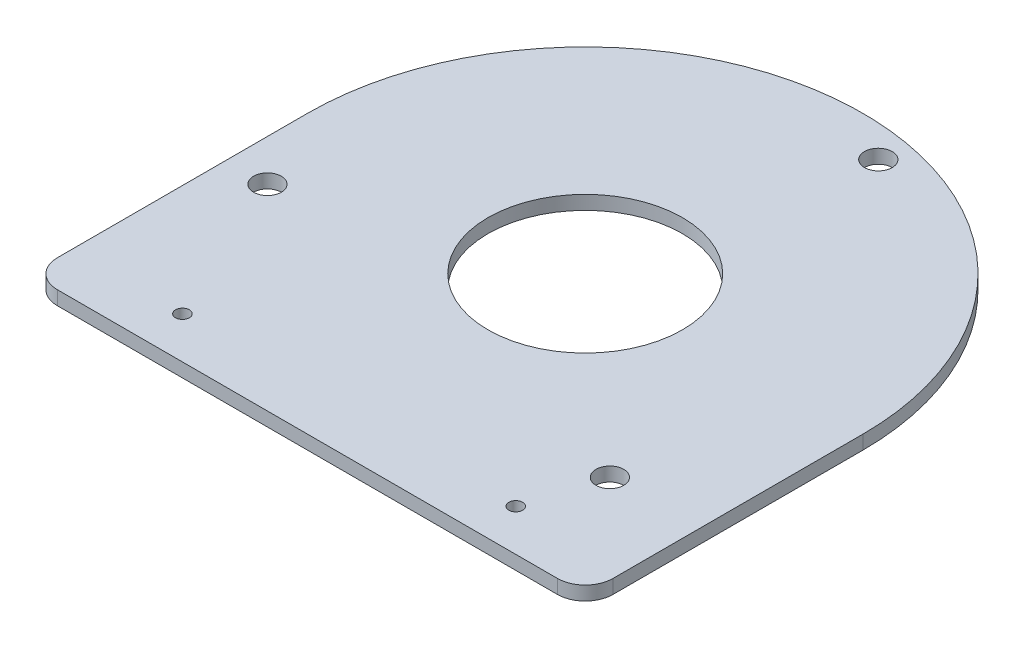
SolidWorks part; units mm, degrees
ref_plane "Front Plane" through (0, 0, 0) normal (0, 0, 1) x (1, 0, 0)
ref_plane "Top Plane" through (0, 0, 0) normal (0, 1, 0) x (1, 0, 0)
ref_plane "Right Plane" through (0, 0, 0) normal (1, 0, 0) x (0, 0, -1)
sketch "Sketch1" plane through (0, 0, 0) normal (0, 1, 0) x (1, 0, 0)
  line L0 (0, 114.3) -> (0, -101.6) construction
  line L1 (127, 0) -> (127, -114.3)
  line L2 (-114.3, -127) -> (114.3, -127)
  line L4 (-127, 0) -> (-127, -114.3)
  line L7 (-127, 0) -> (285.75, 0) construction
  line L8 (0, 0) -> (-127, -43.7296) construction
  circle A0 centre (0, 0) radius 44.45
  circle A1 centre (0, 0) radius 114.3 construction
  circle A2 centre (-108.0728, -37.2124) radius 6.35
  arc A3 (114.3, -127) -> (127, -114.3) centre (114.3, -114.3) ccw
  arc A4 (-127, 0) -> (127, 0) centre (0, 0) cw
  circle A5 centre (21.8095, 112.2) radius 6.35
  circle A6 centre (86.2633, -74.9875) radius 6.35
  arc A7 (-114.3, -127) -> (-127, -114.3) centre (-114.3, -114.3) cw
  circle A8 centre (-76.2, -107.95) radius 3.175
  circle A9 centre (76.2, -107.95) radius 3.175
  point P0 (0, 0)
  point P11 (0, 0)
  point P18 (0, 0)
  point P25 (0, -114.3)
  point P46 (0, 0)
  dimension "D3" = 107.95
  dimension "D5" = 228.6
  dimension "D6" = 12.7
  dimension "D7" = 88.9
  dimension "D9" = 6.35
  dimension "D1" = 76.2
  dimension "D2" = 127
  dimension "D4" = 19
extrude "Boss-Extrude1" add sketch "Sketch1" along normal blind 6.35
sketch "Sketch3" plane through (0, 6.35, 0) normal (0, 1, 0) x (1, 0, 0)
  line L0 (79.375, 127) -> (79.375, -114.3) construction
  line L5 (382.3904, 6.35) -> (-202.4477, 6.35) construction
  line L6 (339.725, -158.75) -> (-180.975, -158.75)
  line L7 (339.725, -158.75) -> (339.725, 171.45)
  line L8 (339.725, 171.45) -> (-180.975, 171.45)
  line L9 (-180.975, -158.75) -> (-180.975, 171.45)
  line L10 (339.725, -158.75) -> (-180.975, 171.45) construction
  line L11 (339.725, 171.45) -> (-180.975, -158.75) construction
  line L27 (-127, 0) -> (-127, -114.3) construction
  line L31 (-127, 0) -> (-127, -114.3)
  point P1 (79.375, 6.35)
  dimension "D1" = 520.7
  dimension "D2" = 206.375
  dimension "D3" = 330.2
sketch "Sketch6" plane through (0, 0, 0) normal (0, 1, 0) x (1, 0, 0)
  circle A0 centre (174.752, 0) radius 14.2875
  circle A2 centre (174.752, 0) radius 11.176
  circle A3 centre (174.752, 0) radius 11.176 construction
  circle A4 centre (174.752, 0) radius 11.176 construction
  dimension "D1" = 28.575
extrude "Cut-Extrude1" cut sketch "Sketch6" along normal blind 28.448
